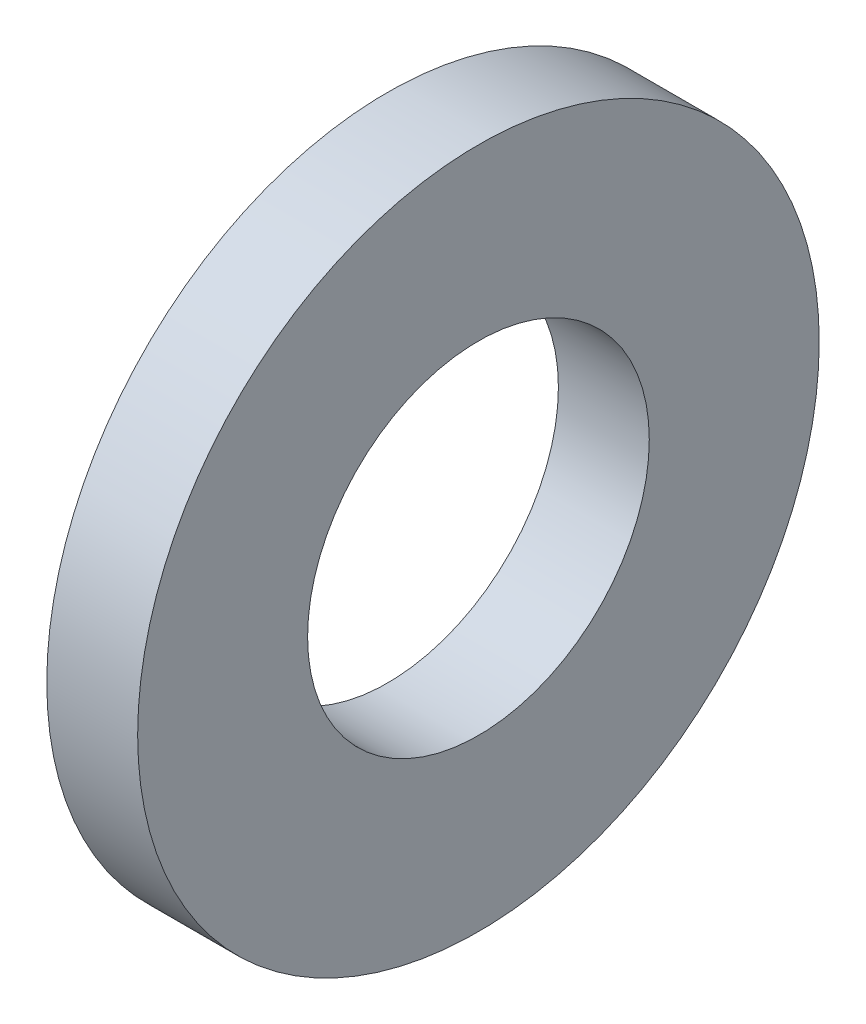
SolidWorks part; units mm, degrees
ref_plane "Front Plane" through (0, 0, 0) normal (0, 0, 1) x (1, 0, 0)
ref_plane "Top Plane" through (0, 0, 0) normal (0, 1, 0) x (1, 0, 0)
ref_plane "Right Plane" through (0, 0, 0) normal (1, 0, 0) x (0, 0, -1)
sketch "Sketch1" plane through (0, 0, 0) normal (1, 0, 0) x (0, 0, -1)
  circle A0 centre (0, 0) radius 2.3813
  circle A1 centre (0, 0) radius 1.1938
  dimension "OD" = 4.7625
  dimension "ID" = 2.3876
extrude "Boss-Extrude1" add sketch "Sketch1" along normal blind 0.635
